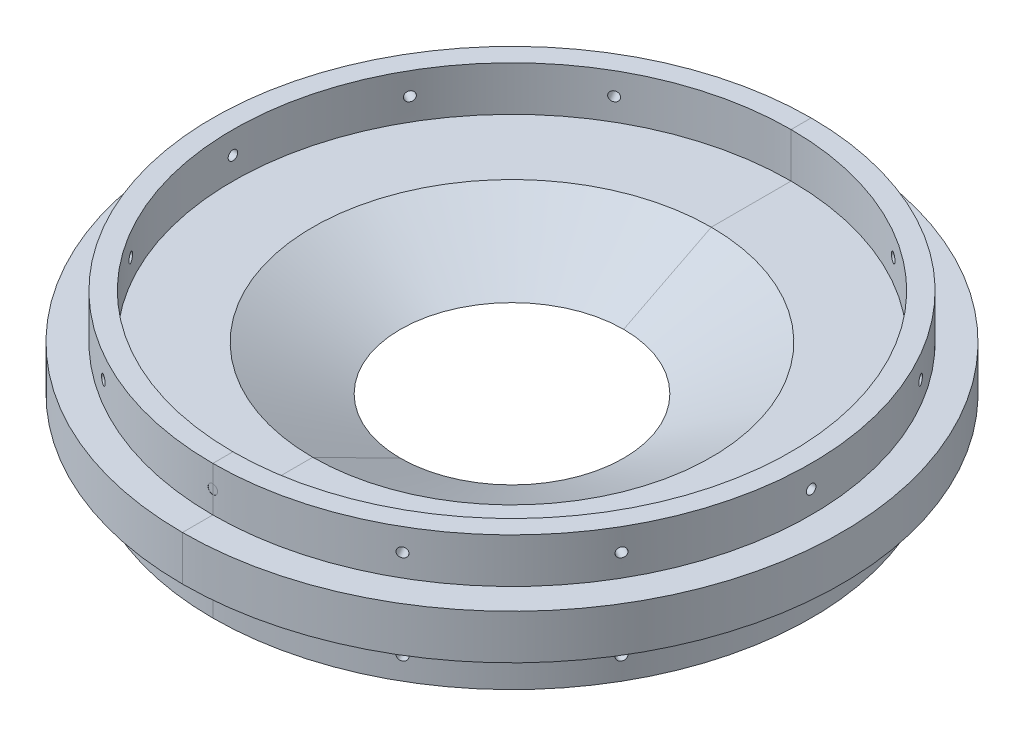
SolidWorks part; units mm, degrees
ref_plane "Front Plane" through (0, 0, 0) normal (0, 0, 1) x (1, 0, 0)
ref_plane "Top Plane" through (0, 0, 0) normal (0, 1, 0) x (1, 0, 0)
ref_plane "Right Plane" through (0, 0, 0) normal (1, 0, 0) x (0, 0, -1)
sketch "Sketch1" plane through (0, 0, 0) normal (0, 1, 0) x (1, 0, 0)
  circle A0 centre (0, 0) radius 93.726
  circle A1 centre (0, 0) radius 31.75
  dimension "D1" = 187.452
  dimension "D2" = 63.5
extrude "Boss-Extrude1" add sketch "Sketch1" along normal mid plane 12.7
sketch "Sketch5" plane through (0, 6.35, 0) normal (0, 1, 0) x (1, 0, 0)
  circle A0 centre (0, 0) radius 85.09
  circle A1 centre (0, 0) radius 79.375
  dimension "D1" = 170.18
  dimension "D2" = 158.75
extrude "Boss-Extrude2" add sketch "Sketch5" along normal blind 12.7
ref_plane "Plane1" through (0, 0, -85.09) normal (0, 0, -1) x (-1, 0, 0)
sketch "Sketch6" plane through (0, 0, -85.09) normal (0, 0, -1) x (-1, 0, 0)
  line L0 (0, 6.985) -> (0, -6.985) construction
  line L1 (93.726, 6.35) -> (-93.726, 6.35) construction
  circle A0 centre (0, 12.7) radius 1.3525
  dimension "D1" = 2.7051
  dimension "D2" = 6.35
extrude "Cut-Extrude1" cut sketch "Sketch6" against normal blind 12.7
pattern_circular "CirPattern1" count 12 over 360 about axis through (0, 6.35, 0) along (0, -1, 0) of "Cut-Extrude1"
mirror "Mirror1" about plane through (0, 0, 0) normal (0, 1, 0) of "CirPattern1", "Cut-Extrude1", "Boss-Extrude2"
sketch "Sketch7" plane through (0, 19.05, 0) normal (0, 1, 0) x (1, 0, 0)
  line L0 (-25.7878, 75.0692) -> (-27.9576, 80.3659)
  line L1 (27.9576, 80.3659) -> (25.7878, 75.0692)
  arc A0 (27.9576, 80.3659) -> (-27.9576, 80.3659) centre (0, -0.672) ccw
  circle A1 centre (0, 0) radius 85.09 construction
  arc A2 (25.7878, 75.0692) -> (-25.7878, 75.0692) centre (0, 0) ccw
  circle A3 centre (0, 0) radius 79.375 construction
extrude "Boss-Extrude3" add sketch "Sketch7" against normal up to surface (25.4 mm away)
mirror "Mirror3" about plane through (0, 0, 0) normal (0, 1, 0) of "Boss-Extrude3"
mirror "Mirror4" about plane through (0, 0, 0) normal (0, 0, 1) of "Boss-Extrude3"
mirror "Mirror5" about plane through (0, 0, 0) normal (0, 1, 0) of "Mirror4"
sketch "Sketch4" plane through (0, 0, 0) normal (0, 0, 1) x (1, 0, 0)
  line L0 (0, 23.2786) -> (0, -14.9525) construction
sketch "Sketch3" plane through (0, 0, 0) normal (0, 0, 1) x (1, 0, 0)
  line L0 (-31.75, -6.35) -> (-56.6752, 6.35)
  line L1 (93.726, 6.35) -> (-93.726, 6.35) construction
  line L2 (-56.6752, 6.35) -> (-31.75, 6.35)
  line L3 (-31.75, 6.35) -> (-31.75, -6.35)
  line L4 (-31.75, -6.35) -> (31.75, -6.35) construction
  line L6 (31.75, 6.35) -> (-31.75, 6.35) construction
  dimension "D1" = 27
revolve "Cut-Revolve1" cut sketch "Sketch3" angle 360 about L0
split "Split1" trim tools "Right Plane" bodies to split 103 resulting bodies 104 105
